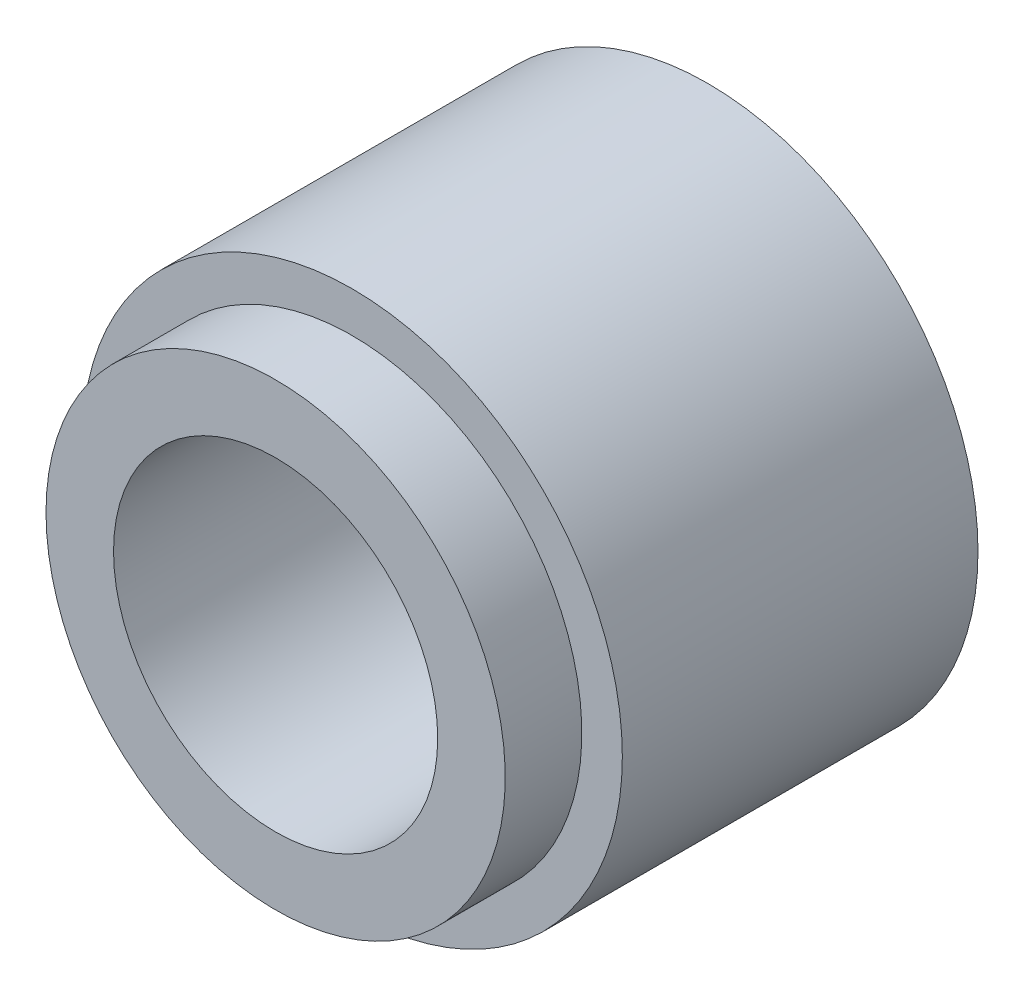
SolidWorks part; units mm, degrees
material "Brass"
ref_plane "Front Plane" through (0, 0, 0) normal (0, 0, 1) x (1, 0, 0)
ref_plane "Top Plane" through (0, 0, 0) normal (0, 1, 0) x (1, 0, 0)
ref_plane "Right Plane" through (0, 0, 0) normal (1, 0, 0) x (0, 0, -1)
sketch "Sketch1" plane through (0, 0, 0) normal (1, 0, 0) x (0, 0, -1)
  line L0 (25.4, 0) -> (-25.4, 0) construction
  line L1 (-25.4, 0) -> (-25.4, 26.9875) construction
  line L2 (-25.4, 26.9875) -> (-16.4, 26.9875)
  line L3 (-16.4, 26.9875) -> (-16.4, 31.75)
  line L4 (-16.4, 31.75) -> (25.4, 31.75)
  line L5 (25.4, 31.75) -> (25.4, 0) construction
  line L6 (-25.4, 26.9875) -> (-25.4, 19.05)
  line L7 (-25.4, 19.05) -> (25.4, 19.05)
  line L8 (25.4, 19.05) -> (25.4, 31.75)
  point P4 (0, 0)
  dimension "D1" = 50.8
  dimension "D2" = 38.1
  dimension "D3" = 53.975
  dimension "D4" = 63.5
revolve "Revolve1" add sketch "Sketch1" angle 360 about L0
